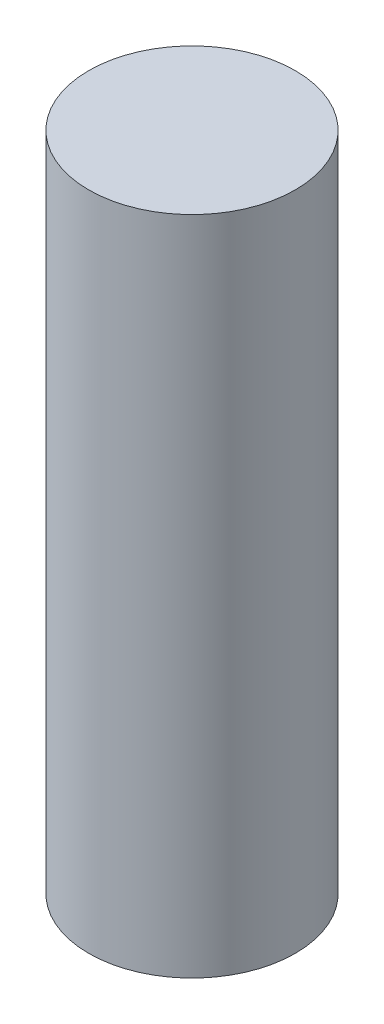
SolidWorks part; units mm, degrees
ref_plane "Front Plane" through (0, 0, 0) normal (0, 0, 1) x (1, 0, 0)
ref_plane "Top Plane" through (0, 0, 0) normal (0, 1, 0) x (1, 0, 0)
ref_plane "Right Plane" through (0, 0, 0) normal (1, 0, 0) x (0, 0, -1)
sketch "Sketch1" plane through (0, 0, 0) normal (0, 1, 0) x (1, 0, 0)
  circle A0 centre (0, 0) radius 3.9688
  dimension "D1" = 7.9375
extrude "Boss-Extrude1" add sketch "Sketch1" along normal blind 25.4
